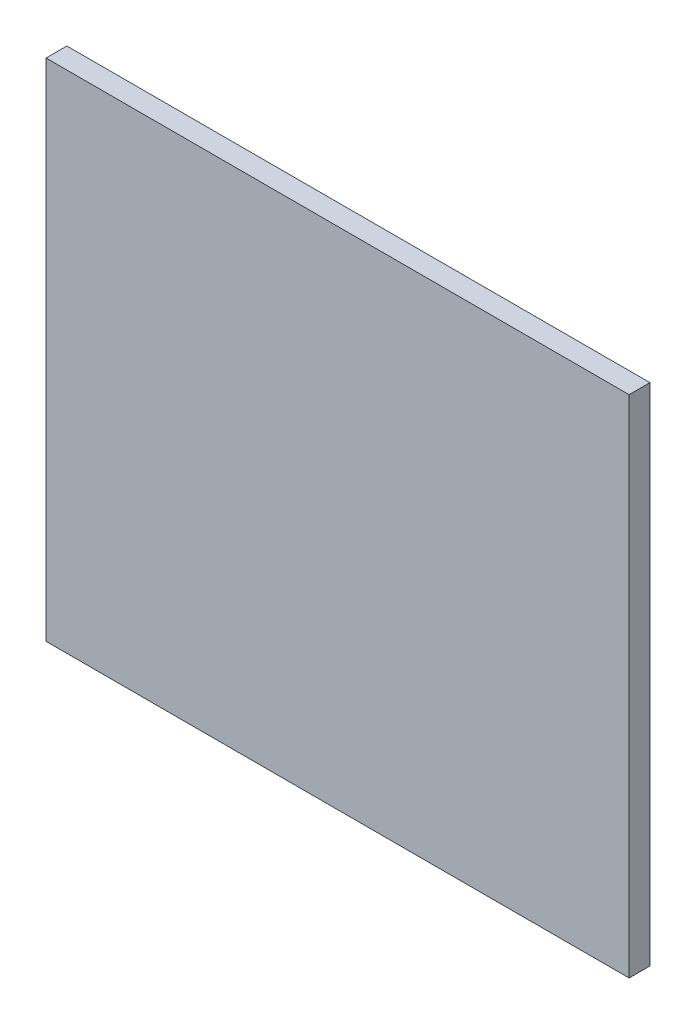
SolidWorks part; units mm, degrees
ref_plane "Front Plane" through (0, 0, 0) normal (0, 0, 1) x (1, 0, 0)
ref_plane "Top Plane" through (0, 0, 0) normal (0, 1, 0) x (1, 0, 0)
ref_plane "Right Plane" through (0, 0, 0) normal (1, 0, 0) x (0, 0, -1)
sketch "Sketch1" plane through (0, 0, 0) normal (0, 0, 1) x (1, 0, 0)
  line L1 (0, 0) -> (355.6, 0)
  line L2 (0, 0) -> (0, 308.102)
  line L3 (0, 308.102) -> (355.6, 308.102)
  line L4 (355.6, 0) -> (355.6, 308.102)
  dimension "D1" = 355.6
  dimension "D2" = 308.102
extrude "Boss-Extrude1" add sketch "Sketch1" along normal blind 12.7
